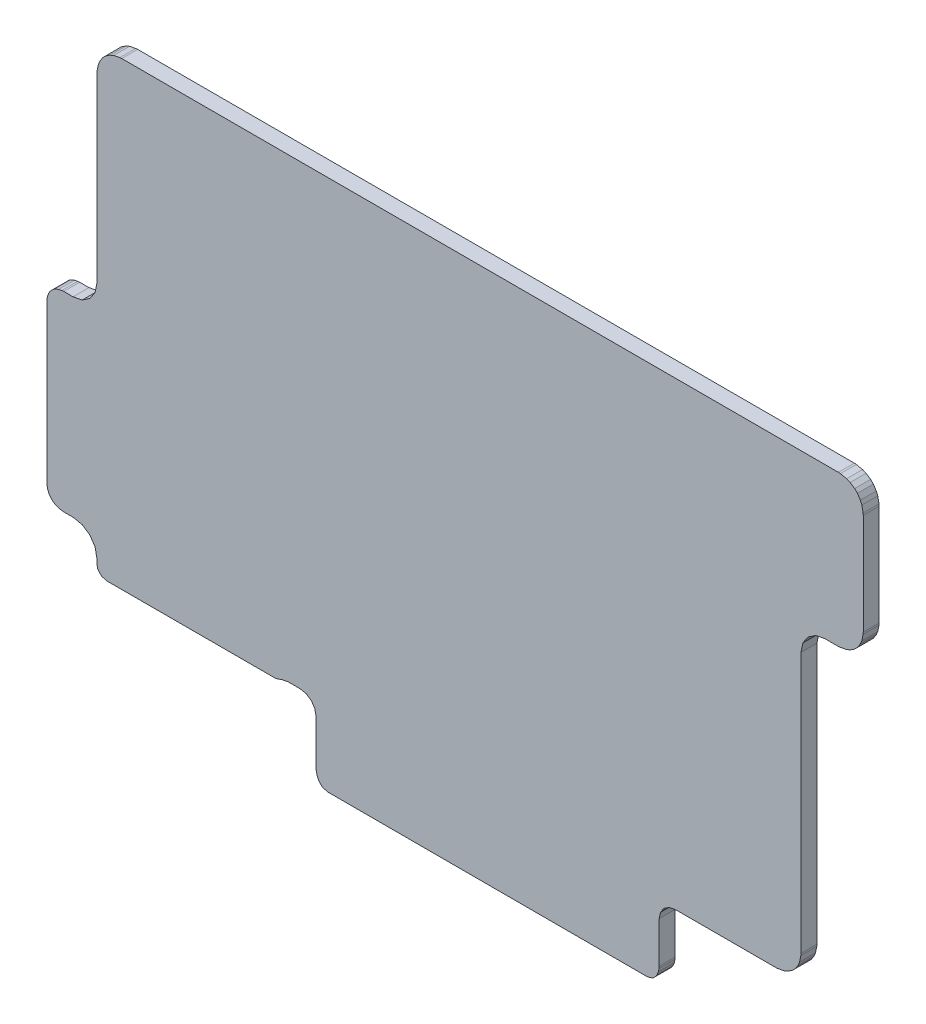
SolidWorks part; units mm, degrees
ref_plane "Front Plane" through (0, 0, 0) normal (0, 0, 1) x (1, 0, 0)
ref_plane "Top Plane" through (0, 0, 0) normal (0, 1, 0) x (1, 0, 0)
ref_plane "Right Plane" through (0, 0, 0) normal (1, 0, 0) x (0, 0, -1)
sketch "Model" plane through (0, 0, 0) normal (0, 0, 1) x (1, 0, 0)
  line L0 (16.018, -7.8968) -> (16.028, -7.9028)
  line L1 (16.028, -7.9028) -> (21.022, -11.5418)
  line L2 (21.022, -11.5418) -> (21.056, -11.5808)
  line L3 (21.056, -11.5808) -> (21.117, -11.6868)
  line L4 (21.117, -11.6868) -> (21.127, -11.7098)
  line L5 (21.127, -11.7098) -> (21.154, -11.7908)
  line L6 (21.154, -11.7908) -> (21.16, -11.8458)
  line L7 (21.16, -11.8458) -> (21.144, -11.9688)
  line L8 (21.144, -11.9688) -> (21.141, -11.9868)
  line L9 (21.141, -11.9868) -> (21.003, -12.4778)
  line L10 (21.003, -12.4778) -> (21.043, -12.8278)
  line L11 (21.043, -12.8278) -> (21.276, -13.2548)
  line L12 (21.276, -13.2548) -> (21.287, -13.2828)
  line L13 (21.287, -13.2828) -> (21.389, -13.6738)
  line L14 (21.389, -13.6738) -> (21.393, -13.7028)
  line L15 (21.393, -13.7028) -> (21.403, -14.1288)
  line L16 (21.403, -14.1288) -> (21.398, -14.1658)
  line L17 (21.398, -14.1658) -> (21.149, -15.0158)
  line L18 (21.149, -15.0158) -> (21.13, -15.0558)
  line L19 (21.13, -15.0558) -> (20.651, -15.6968)
  line L20 (20.651, -15.6968) -> (20.633, -15.7168)
  line L21 (20.633, -15.7168) -> (20.156, -16.1268)
  line L22 (20.156, -16.1268) -> (20.128, -16.1448)
  line L23 (20.128, -16.1448) -> (19.728, -16.3358)
  line L24 (19.728, -16.3358) -> (19.675, -16.3478)
  line L25 (19.675, -16.3478) -> (19.159, -16.3478)
  line L26 (19.159, -16.3478) -> (19.109, -16.3378)
  line L27 (19.109, -16.3378) -> (18.603, -16.1178)
  line L28 (18.603, -16.1178) -> (18.343, -16.0378)
  line L29 (18.343, -16.0378) -> (17.933, -16.1078)
  line L30 (17.933, -16.1078) -> (17.614, -16.4748)
  line L31 (17.614, -16.4748) -> (17.589, -16.4968)
  line L32 (17.589, -16.4968) -> (16.94, -16.9298)
  line L33 (16.94, -16.9298) -> (16.881, -16.9508)
  line L34 (16.881, -16.9508) -> (14.746, -17.1278)
  line L35 (14.746, -17.1278) -> (14.74, -17.1278)
  line L36 (14.74, -17.1278) -> (10.11, -17.1278)
  line L37 (10.11, -17.1278) -> (10.077, -17.1228)
  line L38 (10.077, -17.1228) -> (9.594, -16.9868)
  line L39 (9.594, -16.9868) -> (9.54, -16.9548)
  line L40 (9.54, -16.9548) -> (8.923, -16.3378)
  line L41 (8.923, -16.3378) -> (8.738, -16.3378)
  line L42 (8.738, -16.3378) -> (8.732, -16.3358)
  line L43 (8.732, -16.3358) -> (-8.046, -16.3358)
  line L44 (-8.046, -16.3358) -> (-8.113, -16.3158)
  line L45 (-8.113, -16.3158) -> (-8.159, -16.2638)
  line L46 (-8.159, -16.2638) -> (-8.17, -16.2118)
  line L47 (-8.17, -16.2118) -> (-8.17, -14.2628)
  line L48 (-8.17, -14.2628) -> (-8.151, -14.1958)
  line L49 (-8.151, -14.1958) -> (-8.098, -14.1498)
  line L50 (-8.098, -14.1498) -> (-8.046, -14.1388)
  line L51 (-8.046, -14.1388) -> (8.732, -14.1388)
  line L52 (8.732, -14.1388) -> (8.733, -14.1378)
  line L53 (8.733, -14.1378) -> (8.733, -12.3968)
  line L54 (8.733, -12.3968) -> (8.753, -12.3298)
  line L55 (8.753, -12.3298) -> (8.767, -12.3118)
  line L56 (8.767, -12.3118) -> (9.196, -11.8568)
  line L57 (9.196, -11.8568) -> (9.257, -11.8218)
  line L58 (9.257, -11.8218) -> (9.287, -11.8178)
  line L59 (9.287, -11.8178) -> (11.043, -11.8178)
  line L60 (11.043, -11.8178) -> (11.84, -11.2128)
  line L61 (11.84, -11.2128) -> (11.905, -11.1878)
  line L62 (11.905, -11.1878) -> (11.915, -11.1878)
  line L63 (11.915, -11.1878) -> (13.063, -11.1878)
  line L64 (13.063, -11.1878) -> (13.453, -10.9078)
  line L65 (13.453, -10.9078) -> (15.638, -7.9678)
  line L66 (15.638, -7.9678) -> (15.674, -7.9348)
  line L67 (15.674, -7.9348) -> (15.726, -7.9038)
  line L68 (15.726, -7.9038) -> (15.785, -7.8868)
  line L69 (15.785, -7.8868) -> (15.95, -7.8798)
  line L70 (15.95, -7.8798) -> (16.018, -7.8968)
  line L71 (4.529, 3.2102) -> (4.608, 3.1942)
  line L72 (4.608, 3.1942) -> (4.652, 3.1752)
  line L73 (4.652, 3.1752) -> (4.709, 3.1382)
  line L74 (4.709, 3.1382) -> (4.743, 3.1042)
  line L75 (4.743, 3.1042) -> (4.78, 3.0472)
  line L76 (4.78, 3.0472) -> (4.799, 3.0032)
  line L77 (4.799, 3.0032) -> (4.815, 2.9242)
  line L78 (4.815, 2.9242) -> (4.817, 2.9002)
  line L79 (4.817, 2.9002) -> (4.817, 1.6282)
  line L80 (4.817, 1.6282) -> (4.815, 1.6042)
  line L81 (4.815, 1.6042) -> (4.799, 1.5252)
  line L82 (4.799, 1.5252) -> (4.78, 1.4812)
  line L83 (4.78, 1.4812) -> (4.743, 1.4242)
  line L84 (4.743, 1.4242) -> (4.709, 1.3902)
  line L85 (4.709, 1.3902) -> (4.652, 1.3522)
  line L86 (4.652, 1.3522) -> (4.608, 1.3342)
  line L87 (4.608, 1.3342) -> (4.529, 1.3182)
  line L88 (4.529, 1.3182) -> (4.505, 1.3162)
  line L89 (4.505, 1.3162) -> (4.334, 1.3162)
  line L90 (4.334, 1.3162) -> (4.219, 1.2932)
  line L91 (4.219, 1.2932) -> (4.122, 1.2282)
  line L92 (4.122, 1.2282) -> (4.057, 1.1312)
  line L93 (4.057, 1.1312) -> (4.034, 1.0162)
  line L94 (4.034, 1.0162) -> (4.034, -2.2608)
  line L95 (4.034, -2.2608) -> (4.032, -2.2848)
  line L96 (4.032, -2.2848) -> (4.016, -2.3638)
  line L97 (4.016, -2.3638) -> (3.998, -2.4088)
  line L98 (3.998, -2.4088) -> (3.96, -2.4648)
  line L99 (3.96, -2.4648) -> (3.926, -2.4988)
  line L100 (3.926, -2.4988) -> (3.869, -2.5368)
  line L101 (3.869, -2.5368) -> (3.825, -2.5548)
  line L102 (3.825, -2.5548) -> (3.746, -2.5708)
  line L103 (3.746, -2.5708) -> (3.722, -2.5728)
  line L104 (3.722, -2.5728) -> (2.452, -2.5728)
  line L105 (2.452, -2.5728) -> (2.376, -2.5888)
  line L106 (2.376, -2.5888) -> (2.311, -2.6318)
  line L107 (2.311, -2.6318) -> (2.267, -2.6968)
  line L108 (2.267, -2.6968) -> (2.252, -2.7728)
  line L109 (2.252, -2.7728) -> (2.252, -3.2918)
  line L110 (2.252, -3.2918) -> (2.25, -3.3158)
  line L111 (2.25, -3.3158) -> (2.242, -3.3558)
  line L112 (2.242, -3.3558) -> (2.223, -3.4008)
  line L113 (2.223, -3.4008) -> (2.207, -3.4248)
  line L114 (2.207, -3.4248) -> (2.173, -3.4588)
  line L115 (2.173, -3.4588) -> (2.171, -3.4598)
  line L116 (2.171, -3.4598) -> (2.105, -3.4808)
  line L117 (2.105, -3.4808) -> (2.102, -3.4808)
  line L118 (2.102, -3.4808) -> (-1.915, -3.4778)
  line L119 (-1.915, -3.4778) -> (-1.983, -3.4588)
  line L120 (-1.983, -3.4588) -> (-2.018, -3.4228)
  line L121 (-2.018, -3.4228) -> (-2.033, -3.4008)
  line L122 (-2.033, -3.4008) -> (-2.052, -3.3558)
  line L123 (-2.052, -3.3558) -> (-2.06, -3.3158)
  line L124 (-2.06, -3.3158) -> (-2.062, -3.2918)
  line L125 (-2.062, -3.2918) -> (-2.062, -2.7278)
  line L126 (-2.062, -2.7278) -> (-2.078, -2.6508)
  line L127 (-2.078, -2.6508) -> (-2.121, -2.5868)
  line L128 (-2.121, -2.5868) -> (-2.186, -2.5428)
  line L129 (-2.186, -2.5428) -> (-2.262, -2.5278)
  line L130 (-2.262, -2.5278) -> (-2.417, -2.5278)
  line L131 (-2.417, -2.5278) -> (-2.493, -2.5428)
  line L132 (-2.493, -2.5428) -> (-2.501, -2.5478)
  line L133 (-2.501, -2.5478) -> (-2.568, -2.5688)
  line L134 (-2.568, -2.5688) -> (-2.57, -2.5688)
  line L135 (-2.57, -2.5688) -> (-4.693, -2.5688)
  line L136 (-4.693, -2.5688) -> (-4.76, -2.5498)
  line L137 (-4.76, -2.5498) -> (-4.806, -2.4968)
  line L138 (-4.806, -2.4968) -> (-4.817, -2.4448)
  line L139 (-4.817, -2.4448) -> (-4.817, -2.3878)
  line L140 (-4.817, -2.3878) -> (-4.84, -2.2728)
  line L141 (-4.84, -2.2728) -> (-4.905, -2.1758)
  line L142 (-4.905, -2.1758) -> (-5.002, -2.1108)
  line L143 (-5.002, -2.1108) -> (-5.117, -2.0878)
  line L144 (-5.117, -2.0878) -> (-5.235, -2.0878)
  line L145 (-5.235, -2.0878) -> (-5.259, -2.0858)
  line L146 (-5.259, -2.0858) -> (-5.299, -2.0768)
  line L147 (-5.299, -2.0768) -> (-5.344, -2.0588)
  line L148 (-5.344, -2.0588) -> (-5.368, -2.0428)
  line L149 (-5.368, -2.0428) -> (-5.402, -2.0088)
  line L150 (-5.402, -2.0088) -> (-5.418, -1.9848)
  line L151 (-5.418, -1.9848) -> (-5.437, -1.9398)
  line L152 (-5.437, -1.9398) -> (-5.445, -1.8998)
  line L153 (-5.445, -1.8998) -> (-5.447, -1.8758)
  line L154 (-5.447, -1.8758) -> (-5.447, 0.1002)
  line L155 (-5.447, 0.1002) -> (-5.445, 0.1242)
  line L156 (-5.445, 0.1242) -> (-5.437, 0.1642)
  line L157 (-5.437, 0.1642) -> (-5.418, 0.2092)
  line L158 (-5.418, 0.2092) -> (-5.402, 0.2332)
  line L159 (-5.402, 0.2332) -> (-5.368, 0.2672)
  line L160 (-5.368, 0.2672) -> (-5.344, 0.2832)
  line L161 (-5.344, 0.2832) -> (-5.299, 0.3022)
  line L162 (-5.299, 0.3022) -> (-5.259, 0.3102)
  line L163 (-5.259, 0.3102) -> (-5.235, 0.3122)
  line L164 (-5.235, 0.3122) -> (-5.117, 0.3122)
  line L165 (-5.117, 0.3122) -> (-5.002, 0.3352)
  line L166 (-5.002, 0.3352) -> (-4.905, 0.4002)
  line L167 (-4.905, 0.4002) -> (-4.84, 0.4972)
  line L168 (-4.84, 0.4972) -> (-4.817, 0.6122)
  line L169 (-4.817, 0.6122) -> (-4.817, 2.9002)
  line L170 (-4.817, 2.9002) -> (-4.815, 2.9242)
  line L171 (-4.815, 2.9242) -> (-4.799, 3.0032)
  line L172 (-4.799, 3.0032) -> (-4.78, 3.0472)
  line L173 (-4.78, 3.0472) -> (-4.743, 3.1042)
  line L174 (-4.743, 3.1042) -> (-4.709, 3.1382)
  line L175 (-4.709, 3.1382) -> (-4.652, 3.1752)
  line L176 (-4.652, 3.1752) -> (-4.608, 3.1942)
  line L177 (-4.608, 3.1942) -> (-4.529, 3.2102)
  line L178 (-4.529, 3.2102) -> (-4.505, 3.2122)
  line L179 (-4.505, 3.2122) -> (4.505, 3.2122)
  line L180 (4.505, 3.2122) -> (4.529, 3.2102)
extrude "Boss-Extrude1" add sketch "Model" along normal blind 0.2
delete or keep bodies "Body-Delete/Keep 1" type delete bodies bodies 101
